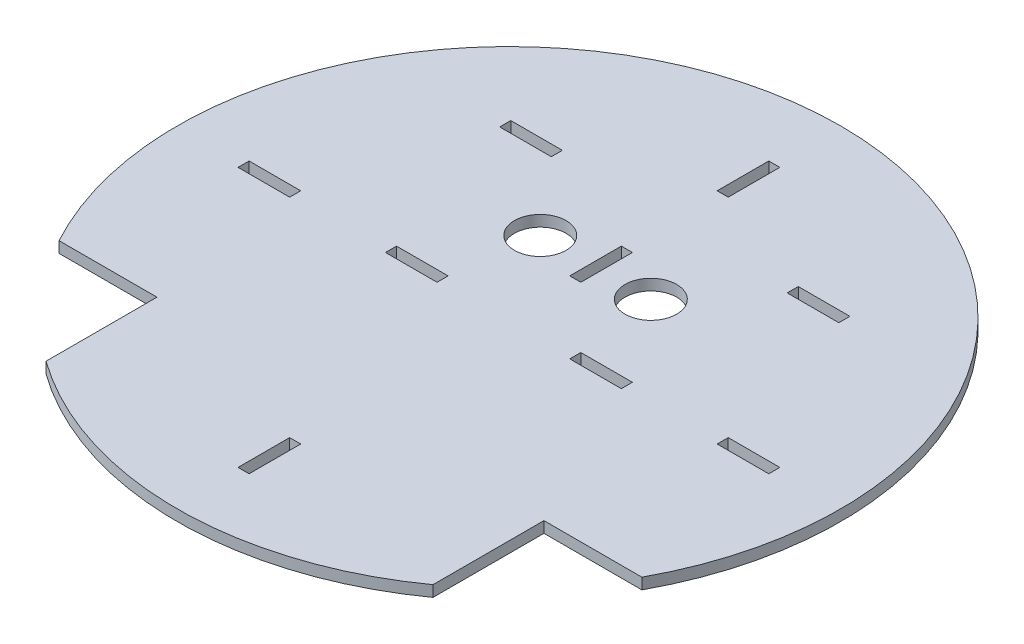
SolidWorks part; units mm, degrees
ref_plane "Front Plane" through (0, 0, 0) normal (0, 0, 1) x (1, 0, 0)
ref_plane "Top Plane" through (0, 0, 0) normal (0, 1, 0) x (1, 0, 0)
ref_plane "Right Plane" through (0, 0, 0) normal (1, 0, 0) x (0, 0, -1)
sketch "Sketch1" plane through (0, 0, 0) normal (0, 1, 0) x (1, 0, 0)
  circle A0 centre (0, 0) radius 90
  dimension "D1" = 180
extrude "Boss-Extrude1" add sketch "Sketch1" along normal blind 3
sketch "Sketch2" plane through (0, 3, 0) normal (0, 1, 0) x (1, 0, 0)
  line L2 (-52.5, -43) -> (-79.0633, -43)
  line L3 (-52.5, -43) -> (-52.5, -73.101)
  circle A0 centre (0, 0) radius 90 construction
  dimension "D1" = 26.5633
  dimension "D2" = 30.101
extrude "Cut-Extrude1" cut sketch "Sketch2" against normal blind 3 and the other way through all flip side to cut
sketch "Sketch3" plane through (0, 3, 0) normal (0, 1, 0) x (1, 0, 0)
  line L2 (52.5, -43) -> (79.0633, -43)
  line L3 (52.5, -43) -> (52.5, -73.101)
  circle A0 centre (0, 0) radius 90 construction
  dimension "D1" = 26.5633
  dimension "D2" = 30.101
extrude "Cut-Extrude2" cut sketch "Sketch3" against normal blind 3 and the other way through all flip side to cut
sketch "Sketch5" plane through (0, 3, 0) normal (0, 1, 0) x (1, 0, 0)
  line L1 (-1.5, 32) -> (1.5, 32)
  line L2 (-1.5, 32) -> (-1.5, 18)
  line L3 (-1.5, 18) -> (1.5, 18)
  line L4 (1.5, 32) -> (1.5, 18)
  point P4 (0, 18)
  dimension "D1" = 14
  dimension "D2" = 3
  dimension "D3" = 18
  dimension "D4" = 18
extrude "Cut-Extrude4" cut sketch "Sketch5" against normal blind 3
sketch "Sketch6" plane through (0, 3, 0) normal (0, 1, 0) x (1, 0, 0)
  line L1 (-1.5, 72) -> (1.5, 72)
  line L2 (-1.5, 72) -> (-1.5, 58)
  line L3 (-1.5, 58) -> (1.5, 58)
  line L4 (1.5, 72) -> (1.5, 58)
  dimension "D1" = 14
  dimension "D2" = 3
  dimension "D3" = 58
  dimension "D4" = 1.5
extrude "Cut-Extrude5" cut sketch "Sketch6" against normal blind 3
sketch "Sketch8" plane through (0, 3, 0) normal (0, 1, 0) x (1, 0, 0)
  line L1 (-1.5, -58) -> (1.5, -58)
  line L2 (-1.5, -58) -> (-1.5, -72)
  line L3 (-1.5, -72) -> (1.5, -72)
  line L4 (1.5, -58) -> (1.5, -72)
  dimension "D1" = 14
  dimension "D2" = 3
  dimension "D3" = 58
  dimension "D4" = 1.5
extrude "Cut-Extrude7" cut sketch "Sketch8" against normal blind 3
sketch "Sketch9" plane through (0, 3, 0) normal (0, 1, 0) x (1, 0, 0)
  line L1 (-32, 1.5) -> (-18, 1.5)
  line L2 (-32, 1.5) -> (-32, -1.5)
  line L3 (-32, -1.5) -> (-18, -1.5)
  line L4 (-18, 1.5) -> (-18, -1.5)
  dimension "D1" = 14
  dimension "D2" = 3
  dimension "D3" = 1.5
  dimension "D4" = 18
extrude "Cut-Extrude8" cut sketch "Sketch9" against normal blind 3
sketch "Sketch10" plane through (0, 3, 0) normal (0, 1, 0) x (1, 0, 0)
  line L1 (-72, 1.5) -> (-58, 1.5)
  line L2 (-72, 1.5) -> (-72, -1.5)
  line L3 (-72, -1.5) -> (-58, -1.5)
  line L4 (-58, 1.5) -> (-58, -1.5)
  dimension "D1" = 14
  dimension "D2" = 3
  dimension "D3" = 1.5
  dimension "D4" = 58
extrude "Cut-Extrude9" cut sketch "Sketch10" against normal blind 3
sketch "Sketch11" plane through (0, 3, 0) normal (0, 1, 0) x (1, 0, 0)
  line L1 (18, 1.5) -> (32, 1.5)
  line L2 (18, 1.5) -> (18, -1.5)
  line L3 (18, -1.5) -> (32, -1.5)
  line L4 (32, 1.5) -> (32, -1.5)
  dimension "D1" = 14
  dimension "D2" = 3
  dimension "D3" = 18
  dimension "D4" = 1.5
extrude "Cut-Extrude10" cut sketch "Sketch11" against normal blind 3
sketch "Sketch12" plane through (0, 3, 0) normal (0, 1, 0) x (1, 0, 0)
  line L1 (58, 1.5) -> (72, 1.5)
  line L2 (58, 1.5) -> (58, -1.5)
  line L3 (58, -1.5) -> (72, -1.5)
  line L4 (72, 1.5) -> (72, -1.5)
  dimension "D1" = 14
  dimension "D2" = 3
  dimension "D3" = 1.5
  dimension "D4" = 58
extrude "Cut-Extrude11" cut sketch "Sketch12" against normal blind 3
sketch "Sketch13" plane through (0, 3, 0) normal (0, 1, 0) x (1, 0, 0)
  line L1 (-46, 46.5) -> (-32, 46.5)
  line L2 (-46, 46.5) -> (-46, 43.5)
  line L3 (-46, 43.5) -> (-32, 43.5)
  line L4 (-32, 46.5) -> (-32, 43.5)
  dimension "D1" = 14
  dimension "D2" = 3
  dimension "D3" = 43.5
  dimension "D4" = 32
extrude "Cut-Extrude12" cut sketch "Sketch13" against normal blind 3
sketch "Sketch14" plane through (0, 3, 0) normal (0, 1, 0) x (1, 0, 0)
  line L1 (46, 46.5) -> (32, 46.5)
  line L2 (46, 46.5) -> (46, 43.5)
  line L3 (46, 43.5) -> (32, 43.5)
  line L4 (32, 46.5) -> (32, 43.5)
  dimension "D1" = 14
  dimension "D2" = 3
  dimension "D3" = 32
  dimension "D4" = 46.5
extrude "Cut-Extrude13" cut sketch "Sketch14" against normal blind 3
sketch "Sketch15" plane through (0, 3, 0) normal (0, 1, 0) x (1, 0, 0)
  line L0 (0, 0) -> (0, 90) construction
  arc A0 (79.0633, -43) -> (-79.0633, -43) centre (0, 0) ccw construction
  circle A1 centre (-15, 23.5) radius 7
  circle A2 centre (15, 23.5) radius 7
extrude "Cut-Extrude14" cut sketch "Sketch15" against normal blind 3
sketch "Sketch17" plane through (0, 3, 0) normal (0, 1, 0) x (1, 0, 0)
  text T0 "HX2" font "Century Gothic" height in points 20
  dimension "D1" = 10
  dimension "D2" = 1.5
